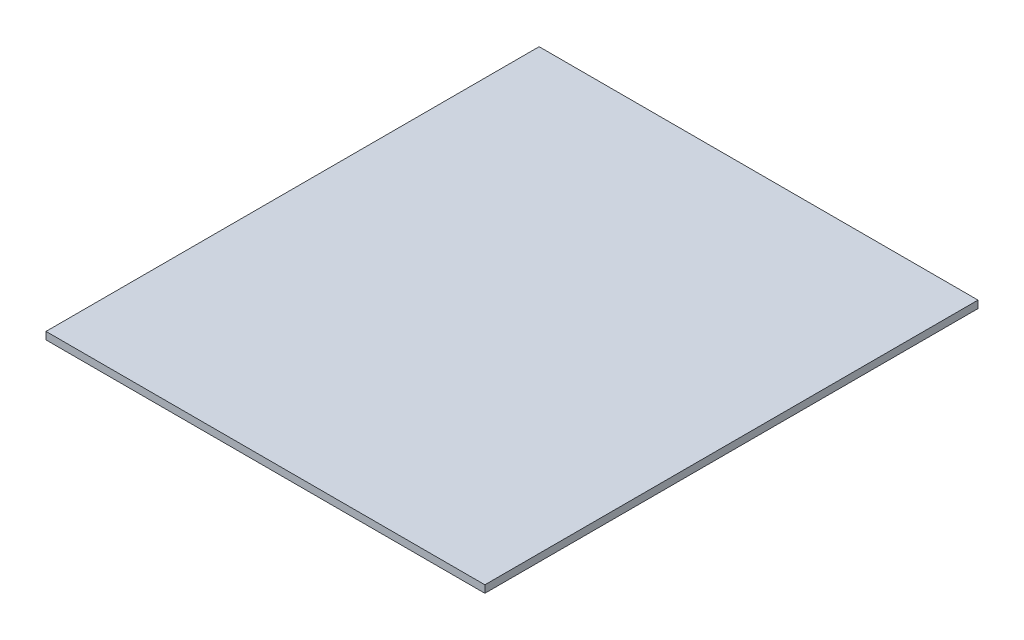
SolidWorks part; units mm, degrees
ref_plane "Plano frontal" through (0, 0, 0) normal (0, 0, 1) x (1, 0, 0)
ref_plane "Plano superior" through (0, 0, 0) normal (0, 1, 0) x (1, 0, 0)
ref_plane "Plano direito" through (0, 0, 0) normal (1, 0, 0) x (0, 0, -1)
sketch "Esboço1" plane through (0, 0, 0) normal (0, 1, 0) x (1, 0, 0)
  line L0 (0, 100) -> (0, -100) construction
  line L1 (-89, 100) -> (89, 100)
  line L2 (-89, 100) -> (-89, -100)
  line L3 (-89, -100) -> (89, -100)
  line L4 (89, 100) -> (89, -100)
  line L5 (-89, 0) -> (89, 0) construction
  point P8 (0, 0)
  dimension "D1" = 178
  dimension "D2" = 200
extrude "Ressalto-extrusão1" add sketch "Esboço1" along normal blind 3
